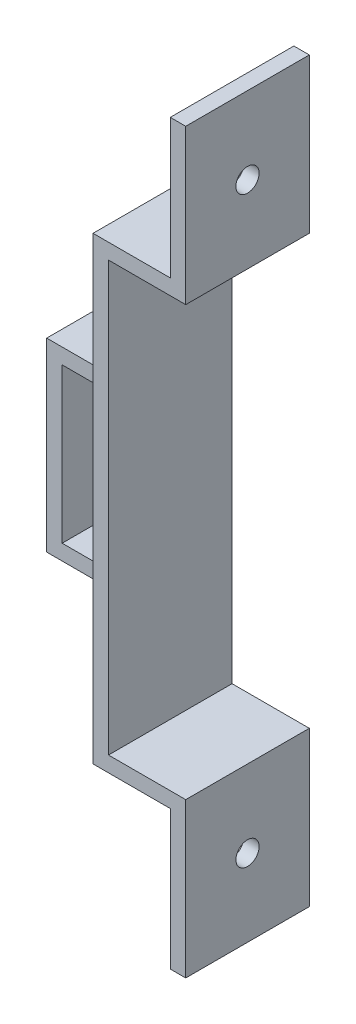
SolidWorks part; units mm, degrees
ref_plane "Ön Düzlem" through (0, 0, 0) normal (0, 0, 1) x (1, 0, 0)
ref_plane "Üst Düzlem" through (0, 0, 0) normal (0, 1, 0) x (1, 0, 0)
ref_plane "Sağ Düzlem" through (0, 0, 0) normal (1, 0, 0) x (0, 0, -1)
sketch "Çizim1" plane through (0, 0, 0) normal (0, 0, 1) x (1, 0, 0)
  line L0 (-23, 0) -> (-13, 0) construction
  line L5 (-13, 27.75) -> (-23, 27.75)
  line L6 (-23, 27.75) -> (-23, -27.75)
  line L7 (-23, -27.75) -> (-13, -27.75)
  line L9 (-25, 29.75) -> (-25, -29.75)
  line L10 (-25, -29.75) -> (-15, -29.75)
  line L13 (-23, 0) -> (-13, 0)
  line L20 (-13, 27.75) -> (-13, 29.75)
  line L27 (23.0087, 29.75) -> (-25, 29.75) construction
  line L28 (23.0087, 27.75) -> (-23, 27.75) construction
  line L29 (-25, -29.75) -> (23.0087, -29.75) construction
  line L30 (-23, -27.75) -> (23.0087, -27.75) construction
  line L32 (-13, -27.75) -> (-13, -29.75)
  line L33 (-15, 29.75) -> (-25, 29.75)
  line L34 (-15, 27.75) -> (-13, 27.75)
  line L35 (-15, 29.75) -> (-15, 47.75)
  line L36 (-15, 47.75) -> (-13, 47.75)
  line L44 (-13, 27.75) -> (-13, 47.75)
  line L45 (-15, 27.75) -> (-13, 47.75) construction
  line L46 (-15, 47.75) -> (-13, 27.75) construction
  line L47 (-15, -47.75) -> (-13, -47.75)
  line L48 (-15, -47.75) -> (-15, -29.75)
  line L49 (-15, -27.75) -> (-13, -27.75)
  line L50 (-13, -47.75) -> (-13, -27.75)
  line L51 (-15, -47.75) -> (-13, -27.75) construction
  line L52 (-15, -27.75) -> (-13, -47.75) construction
  point P1 (-14, 37.75)
  point P11 (0, 0)
  point P16 (0, 0)
  point P17 (-13, -28.2506)
  point P18 (-14, -37.75)
  point P19 (-15.4231, 27.75)
  point P27 (-15.6766, -27.75)
  dimension "D1" = 27.75
  dimension "D2" = 27.75
  dimension "D3" = 2
  dimension "D4" = 10
  dimension "D5" = 20
  dimension "D12" = 10
  dimension "D13" = 10
  dimension "D14" = 55.5
  dimension "D6" = 2
extrude "Yükseklik-Ekstrüzyon1" add sketch "Çizim1" along normal mid plane 16
sketch "Çizim2" plane through (-15, 0, 0) normal (-1, 0, 0) x (0, 0, 1)
  line L0 (8, 47.75) -> (-8, 47.75) construction
  line L2 (8, -27.75) -> (-8, -27.75) construction
  circle A0 centre (0, 37.75) radius 1.5
  circle A1 centre (0, -37.75) radius 1.5
  dimension "D3" = 3
  dimension "D1" = 10
  dimension "D2" = 10
extrude "Kes-Ekstrüzyon1" cut sketch "Çizim2" against normal blind 10
sketch "Çizim4" plane through (0, 0, 0) normal (0, 0, 1) x (1, 0, 0)
  line L0 (-32, 0) -> (-16.1588, 0) construction
  line L1 (-25, 10) -> (-32, 10)
  line L2 (-25, 29.75) -> (-25, -29.75) construction
  line L3 (-32, 10) -> (-32, -10)
  line L4 (-32, -10) -> (-25, -10)
  line L5 (-25, 12) -> (-34, 12)
  line L6 (-34, 12) -> (-34, -12)
  line L7 (-34, -12) -> (-25, -12)
  line L8 (-25, 12) -> (-25, 10)
  line L9 (-25, -10) -> (-25, -12)
  dimension "D1" = 20
  dimension "D2" = 10
  dimension "D3" = 7
  dimension "D4" = 2
extrude "Yükseklik-Ekstrüzyon2" add sketch "Çizim4" along normal mid plane 10
